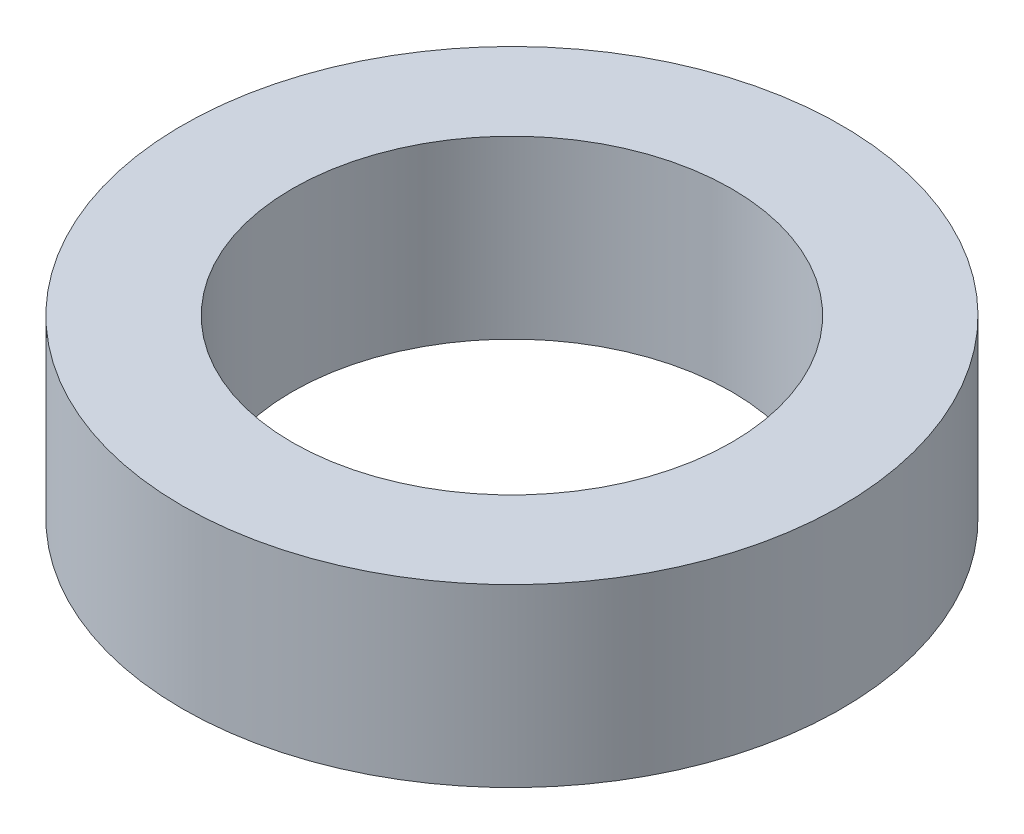
SolidWorks part; units mm, degrees
ref_plane "Front Plane" through (0, 0, 0) normal (0, 0, 1) x (1, 0, 0)
ref_plane "Top Plane" through (0, 0, 0) normal (0, 1, 0) x (1, 0, 0)
ref_plane "Right Plane" through (0, 0, 0) normal (1, 0, 0) x (0, 0, -1)
sketch "Sketch1" plane through (0, 0, 0) normal (0, 1, 0) x (1, 0, 0)
  circle A0 centre (0, 0) radius 7.5
  circle A1 centre (0, 0) radius 5
  dimension "D1" = 10
  dimension "D2" = 15
extrude "Boss-Extrude1" add sketch "Sketch1" along normal blind 4
